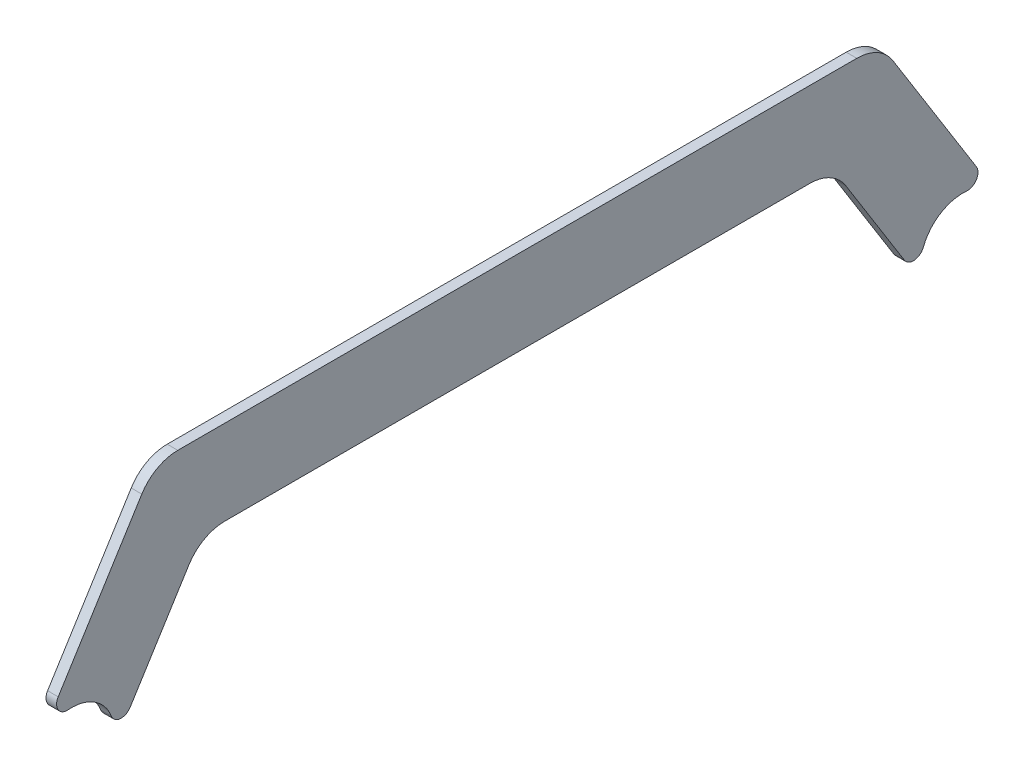
SolidWorks part; units mm, degrees
ref_plane "Front Plane" through (0, 0, 0) normal (0, 0, 1) x (1, 0, 0)
ref_plane "Top Plane" through (0, 0, 0) normal (0, 1, 0) x (1, 0, 0)
ref_plane "Right Plane" through (0, 0, 0) normal (1, 0, 0) x (0, 0, -1)
sketch "Sketch1" plane through (48.3855, 0, 0) normal (1, 0, 0) x (0, 0, -1)
  line L0 (-136.5916, 140.1844) -> (130.1084, 140.1844) construction
  line L1 (-136.5916, 140.1844) -> (130.1084, 140.1844) construction
  line L2 (-147.3612, 146.9154) -> (-125.822, 133.4534) construction
  line L3 (119.3388, 133.4534) -> (140.878, 146.9154) construction
  line L6 (98.3584, 190.9844) -> (130.1084, 140.1844) construction
  line L7 (-104.8416, 190.9844) -> (98.3584, 190.9844) construction
  line L8 (-136.5916, 140.1844) -> (-104.8416, 190.9844) construction
  line L9 (98.3584, 190.9844) -> (130.1084, 140.1844) construction
  line L10 (-104.8416, 190.9844) -> (98.3584, 190.9844) construction
  line L11 (-136.5916, 140.1844) -> (-104.8416, 190.9844) construction
  line L12 (-147.3612, 146.9154) -> (-111.8806, 203.6844)
  line L13 (-111.8806, 203.6844) -> (105.3973, 203.6844)
  line L14 (105.3973, 203.6844) -> (140.878, 146.9154)
  line L15 (119.3388, 133.4534) -> (91.3194, 178.2844)
  line L16 (91.3194, 178.2844) -> (-97.8027, 178.2844)
  line L17 (-97.8027, 178.2844) -> (-125.822, 133.4534)
  line L18 (-3.2416, 203.6844) -> (-3.2416, 178.2844) construction
  arc A0 (-147.3612, 146.9154) -> (-125.822, 133.4534) centre (-136.5916, 140.1844) cw
  arc A1 (140.878, 146.9154) -> (119.3388, 133.4534) centre (130.1084, 140.1844) ccw
  point P17 (-3.2416, 190.9844)
  dimension "D1" = 12.7
  dimension "D2" = 25.4
extrude "Boss-Extrude1" add sketch "Sketch1" along normal blind 3.175
fillet "Fillet1" radius 3.175 4 edges at (49.973, 146.9154, -140.878) (49.973, 133.4534, -119.3388) (49.973, 133.4534, 125.822) (49.973, 146.9154, 147.3612)
fillet "Fillet2" radius 12.7 4 edges at (49.973, 203.6844, -105.3973) (49.973, 178.2844, -91.3194) (49.973, 178.2844, 97.8027) (49.973, 203.6844, 111.8806)
